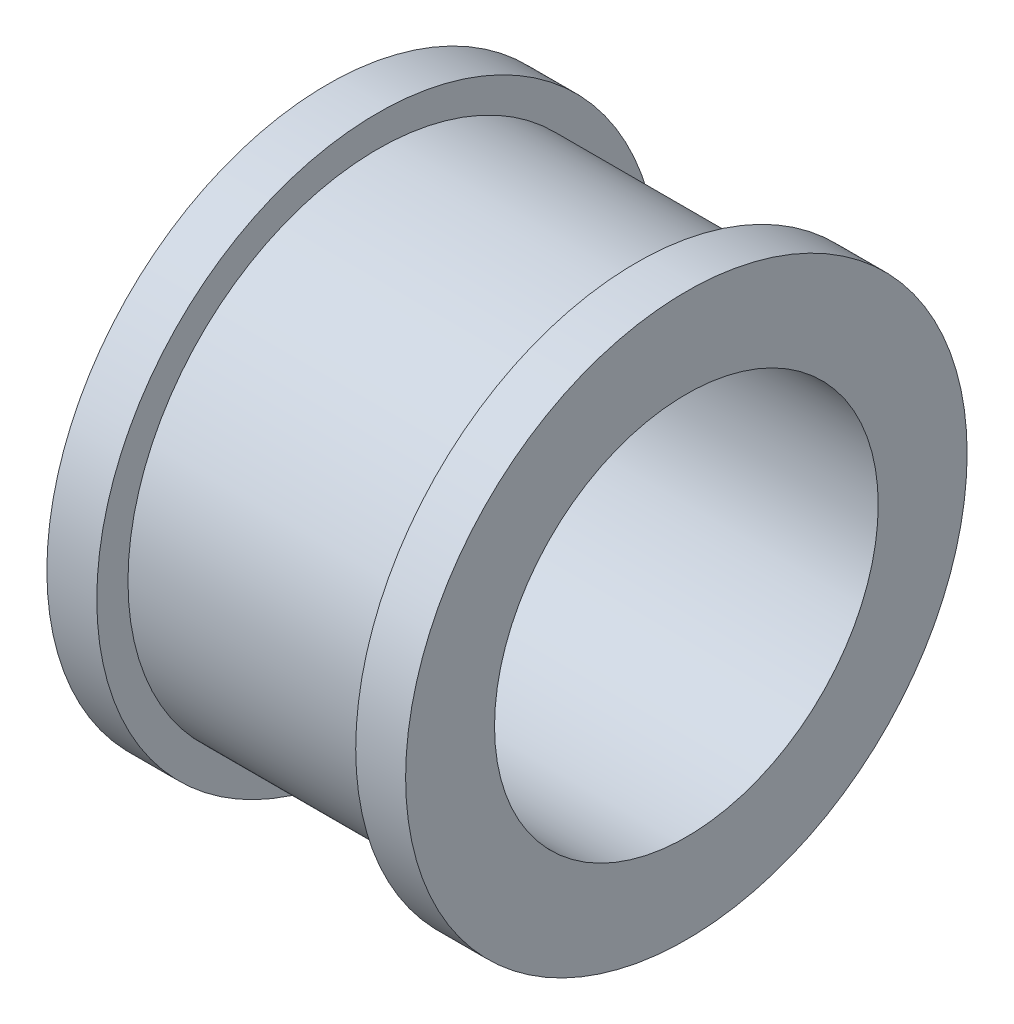
SolidWorks part; units mm, degrees
material "ABS"
ref_plane "Front Plane" through (0, 0, 0) normal (0, 0, 1) x (1, 0, 0)
ref_plane "Top Plane" through (0, 0, 0) normal (0, 1, 0) x (1, 0, 0)
ref_plane "Right Plane" through (0, 0, 0) normal (1, 0, 0) x (0, 0, -1)
sketch "Sketch1" plane through (0, 0, 0) normal (0, 0, 1) x (1, 0, 0)
  line L0 (0, 0) -> (8.902, 0) construction
  line L1 (-2.875, 1.5) -> (-2.875, 4.5)
  line L2 (-2.075, 4.5) -> (-2.075, 4)
  line L3 (-2.075, 4) -> (2.075, 4)
  line L4 (2.075, 4) -> (2.075, 4.5)
  line L5 (2.875, 4.5) -> (2.875, 1.5)
  line L6 (2.875, 1.5) -> (-2.875, 1.5)
  line L7 (0, 1.5) -> (0, 0) construction
  line L8 (-2.875, 4.5) -> (-2.075, 4.5)
  line L9 (2.075, 4.5) -> (2.875, 4.5)
  line L10 (0, 4) -> (0, 1.5) construction
  dimension "D1" = 4
  dimension "D2" = 1.5
  dimension "D4" = 5.75
  dimension "D5" = 4.15
  dimension "D6" = 4.5
revolve "Revolve1" add sketch "Sketch1" angle 360 about L0
sketch "Sketch3" plane through (0, 0, 0) normal (1, 0, 0) x (0, 0, -1)
  circle A0 centre (0, 0) radius 3.075
  dimension "D1" = 6.15
extrude "Cut-Extrude1" cut sketch "Sketch3" along normal through all and the other way through all
